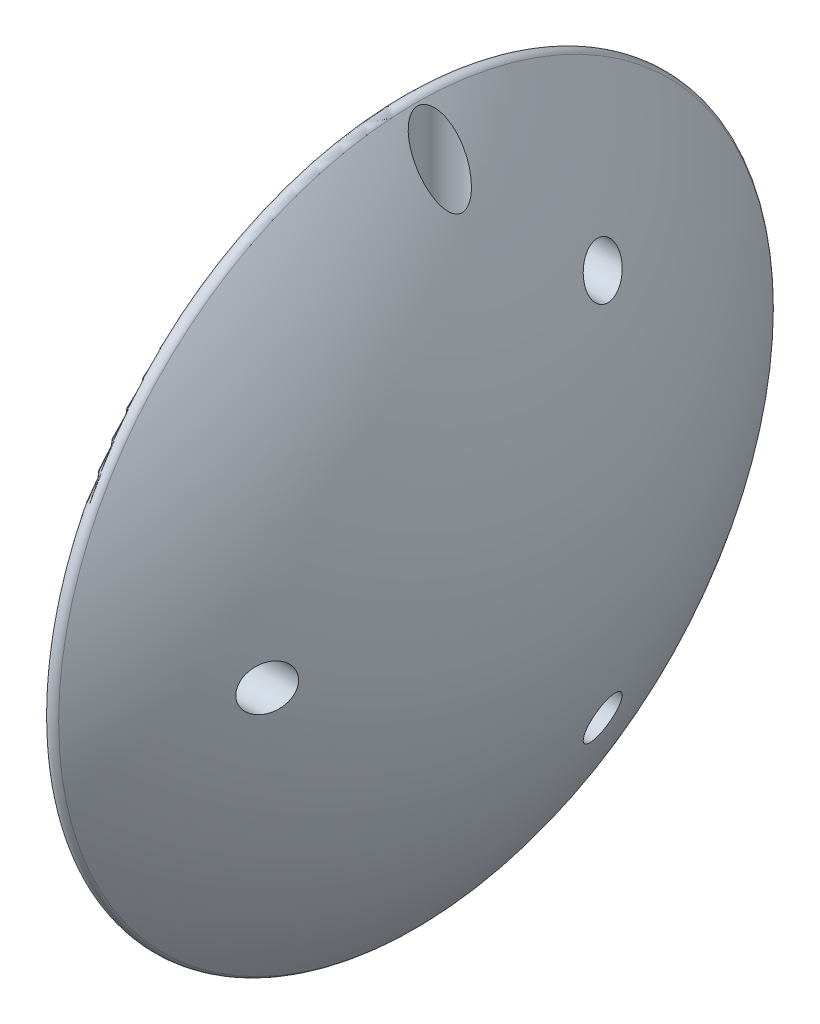
SolidWorks part; units mm, degrees
material "3D_printed_PLA"
ref_plane "Front Plane" through (0, 0, 0) normal (0, 0, 1) x (1, 0, 0)
ref_plane "Top Plane" through (0, 0, 0) normal (0, 1, 0) x (1, 0, 0)
ref_plane "Right Plane" through (0, 0, 0) normal (1, 0, 0) x (0, 0, -1)
sketch "Sketch1" plane through (0, 0, 0) normal (0, 0, 1) x (1, 0, 0)
  line L0 (62.25, 50.2488) -> (62.25, 0)
  line L1 (62.25, 0) -> (80, 0)
  arc A0 (62.25, 50.2488) -> (80, 0) centre (0, 0) cw
  dimension "D1" = 80
  dimension "D2" = 62.25
revolve "Revolve1" add sketch "Sketch1" angle 360 about L1
sketch "Sketch2" plane through (62.25, 0, 0) normal (-1, 0, 0) x (0, 0, 1)
  line L0 (-1.3229, 1.5) -> (1.3229, 1.5)
  arc A0 (-1.3229, 1.5) -> (1.3229, 1.5) centre (0, 0) ccw
  point P4 (0, -2)
  point P5 (1.5048, 1.3174)
  dimension "D1" = 2
  dimension "D2" = 3.5
extrude "Cut-Extrude1" cut sketch "Sketch2" against normal blind 15
sketch "Sketch3" plane through (0, 1.5, 0) normal (0, -1, 0) x (1, 0, 0)
  line L0 (62.25, 1.3229) -> (62.25, -1.3229) construction
  line L1 (77.25, 0) -> (67.25, 0) construction
  line L2 (77.25, 1.3229) -> (77.25, -1.3229) construction
  circle A0 centre (67.25, 0) radius 1.4
  point P4 (67.1262, 0.3783)
  dimension "D2" = 2.8
  dimension "D1" = 5
extrude "Cut-Extrude2" cut sketch "Sketch3" against normal through all
sketch "Sketch4" plane through (0, 1.5, 0) normal (0, -1, 0) x (1, 0, 0)
  circle A0 centre (67.25, 0) radius 3
  dimension "D1" = 6
extrude "Cut-Extrude3" cut sketch "Sketch4" against normal through all from offset 20 offset against normal yes
fillet "Fillet1" radius 1 1 edges at (62.25, 0, 50.2488)
chamfer "Chamfer1" distance 1 angle 45 2 edges at (62.25, 1.5, 0) (62.25, -2, 0)
sketch "Sketch5" plane through (62.25, 0, 0) normal (-1, 0, 0) x (0, 0, 1)
  circle A0 centre (-15, -25.9808) radius 1.4 construction
  circle A1 centre (30, 0) radius 1.4 construction
  circle A2 centre (-15, 25.9808) radius 1.4 construction
  circle A3 centre (-15, -25.9808) radius 1.4
  circle A4 centre (30, 0) radius 1.4
  circle A5 centre (-15, 25.9808) radius 1.4
extrude "Cut-Extrude4" cut sketch "Sketch5" against normal through all both and the other way through all
sketch "Sketch6" plane through (62.25, 0, 0) normal (-1, 0, 0) x (0, 0, 1)
  circle A0 centre (-15, 25.9808) radius 3
  circle A1 centre (30, 0) radius 3
  circle A2 centre (-15, -25.9808) radius 3
  dimension "D1" = 6
extrude "Cut-Extrude5" cut sketch "Sketch6" against normal blind 10 from offset 5
